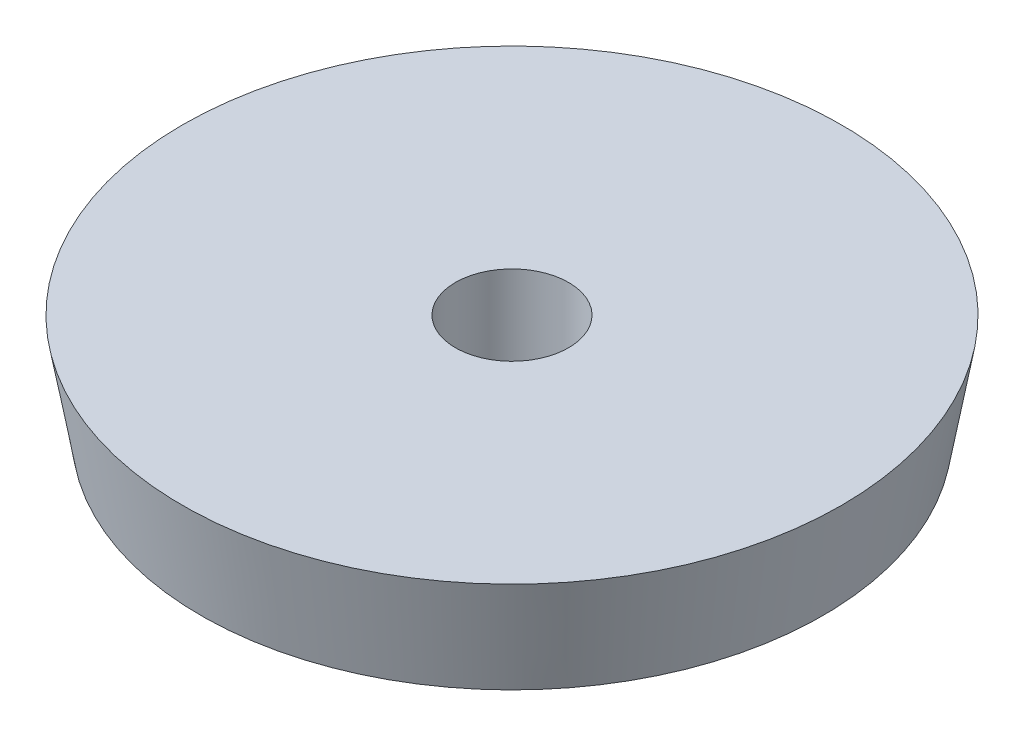
SolidWorks part; units mm, degrees
ref_plane "Front Plane" through (0, 0, 0) normal (0, 0, 1) x (1, 0, 0)
ref_plane "Top Plane" through (0, 0, 0) normal (0, 1, 0) x (1, 0, 0)
ref_plane "Right Plane" through (0, 0, 0) normal (1, 0, 0) x (0, 0, -1)
sketch "Sketch1" plane through (0, 0, 0) normal (0, 0, 1) x (1, 0, 0)
  line L0 (0, 0) -> (0, -63.5)
  line L1 (0, -63.5) -> (188.8032, -63.5)
  line L2 (188.8032, -63.5) -> (200, 0)
  line L3 (200, 0) -> (0, 0)
  dimension "D1" = 100
  dimension "D2" = 200
  dimension "D3" = 63.5
revolve "Revolve1" add sketch "Sketch1" angle 360 about L0
sketch "Sketch2" plane through (0, 0, 0) normal (0, 1, 0) x (1, 0, 0)
  circle A0 centre (0, 0) radius 34.3535
  dimension "D1" = 68.707
extrude "Cut-Extrude1" cut sketch "Sketch2" against normal through all
